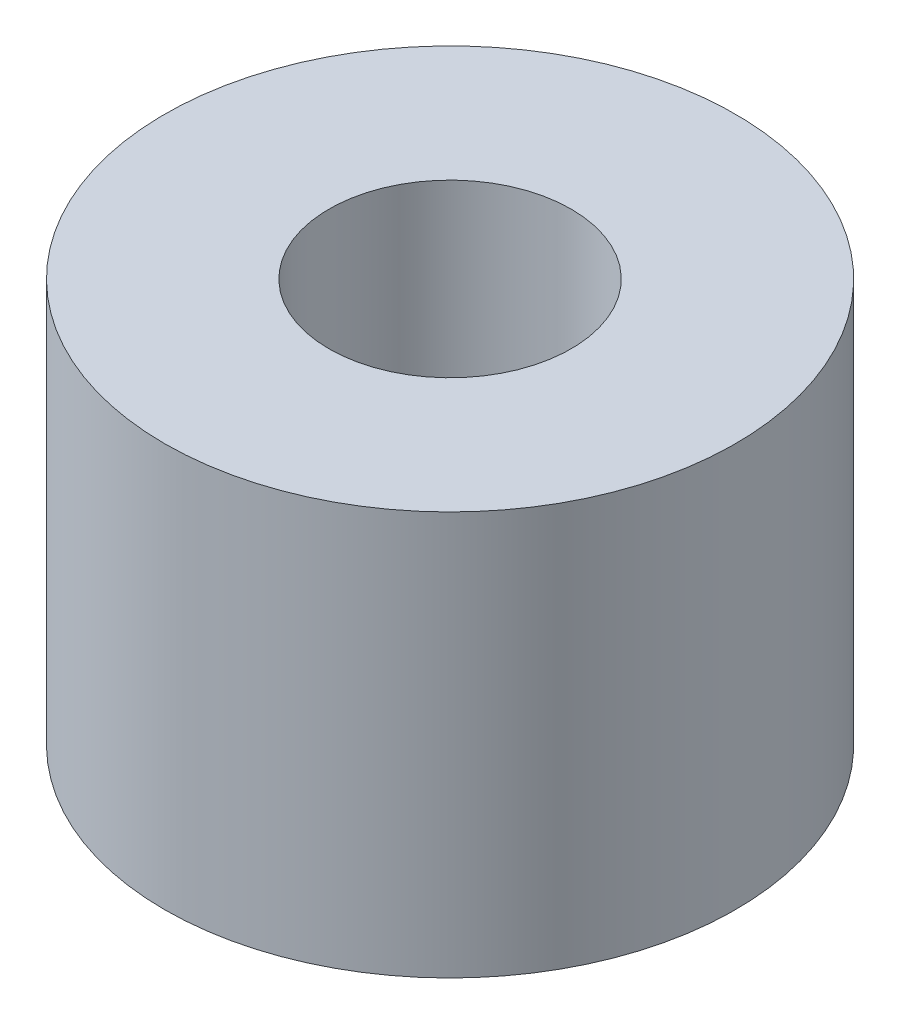
SolidWorks part; units mm, degrees
ref_plane "Front Plane" through (0, 0, 0) normal (0, 0, 1) x (1, 0, 0)
ref_plane "Top Plane" through (0, 0, 0) normal (0, 1, 0) x (1, 0, 0)
ref_plane "Right Plane" through (0, 0, 0) normal (1, 0, 0) x (0, 0, -1)
sketch "Sketch1" plane through (0, 0, 0) normal (0, 1, 0) x (1, 0, 0)
  circle A1 centre (0, 0) radius 1.5
  circle A2 centre (0, 0) radius 3.5355
extrude "Boss-Extrude1" add sketch "Sketch1" along normal blind 5
